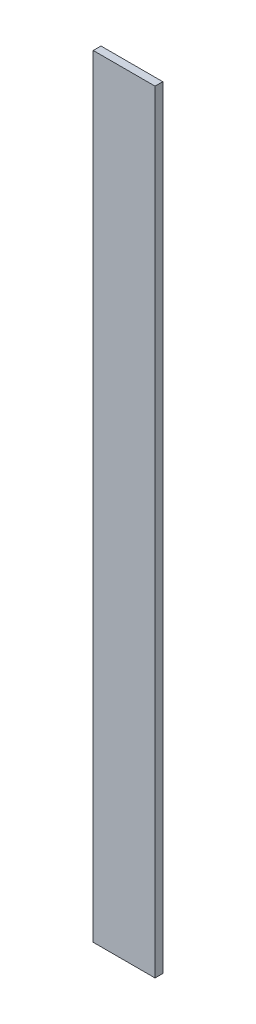
SolidWorks part; units mm, degrees
ref_plane "Front Plane" through (0, 0, 0) normal (0, 0, 1) x (1, 0, 0)
ref_plane "Top Plane" through (0, 0, 0) normal (0, 1, 0) x (1, 0, 0)
ref_plane "Right Plane" through (0, 0, 0) normal (1, 0, 0) x (0, 0, -1)
sketch "Sketch1" plane through (0, 0, 0) normal (0, 1, 0) x (1, 0, 0)
  line L1 (0, 0) -> (50.8, 0)
  line L2 (0, 0) -> (0, -6.35)
  line L3 (0, -6.35) -> (50.8, -6.35)
  line L4 (50.8, 0) -> (50.8, -6.35)
  dimension "D2" = 50.8
  dimension "D3" = 6.35
extrude "Boss-Extrude1" add sketch "Sketch1" along normal mid plane 635
